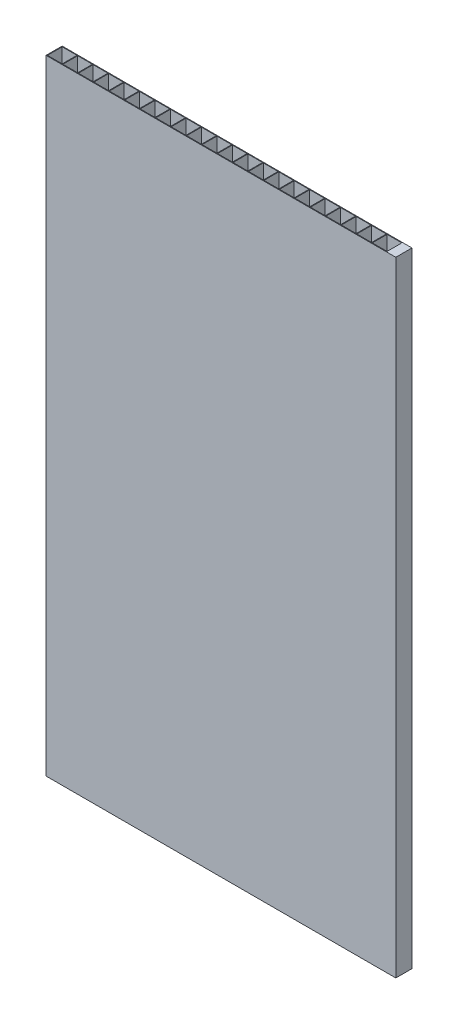
SolidWorks part; units mm, degrees
material "Perspex (TM) GS Acrylic Cast Sheet"
ref_plane "Front Plane" through (0, 0, 0) normal (0, 0, 1) x (1, 0, 0)
ref_plane "Top Plane" through (0, 0, 0) normal (0, 1, 0) x (1, 0, 0)
ref_plane "Right Plane" through (0, 0, 0) normal (1, 0, 0) x (0, 0, -1)
sketch "Sketch1" plane through (0, 0, 0) normal (0, 1, 0) x (1, 0, 0)
  line L0 (6, 5.75) -> (6, 0.25)
  line L1 (0, 0) -> (130, 0)
  line L2 (0, 0) -> (0, 6)
  line L3 (0, 6) -> (130, 6)
  line L4 (130, 0) -> (130, 6)
  line L5 (0.25, 5.75) -> (5.75, 5.75)
  line L6 (0.25, 5.75) -> (0.25, 0.25)
  line L7 (0.25, 0.25) -> (5.75, 0.25)
  line L8 (5.75, 5.75) -> (5.75, 0.25)
  line L9 (6, 5.75) -> (11.5, 5.75)
  line L10 (11.5, 5.75) -> (11.5, 0.25)
  line L11 (6, 0.25) -> (11.5, 0.25)
  line L12 (11.75, 5.75) -> (11.75, 0.25)
  line L13 (11.75, 5.75) -> (17.25, 5.75)
  line L14 (17.25, 5.75) -> (17.25, 0.25)
  line L15 (11.75, 0.25) -> (17.25, 0.25)
  line L16 (17.5, 5.75) -> (17.5, 0.25)
  line L17 (17.5, 5.75) -> (23, 5.75)
  line L18 (23, 5.75) -> (23, 0.25)
  line L19 (17.5, 0.25) -> (23, 0.25)
  line L20 (23.25, 5.75) -> (23.25, 0.25)
  line L21 (23.25, 5.75) -> (28.75, 5.75)
  line L22 (28.75, 5.75) -> (28.75, 0.25)
  line L23 (23.25, 0.25) -> (28.75, 0.25)
  line L24 (29, 5.75) -> (29, 0.25)
  line L25 (29, 5.75) -> (34.5, 5.75)
  line L26 (34.5, 5.75) -> (34.5, 0.25)
  line L27 (29, 0.25) -> (34.5, 0.25)
  line L28 (34.75, 5.75) -> (34.75, 0.25)
  line L29 (34.75, 5.75) -> (40.25, 5.75)
  line L30 (40.25, 5.75) -> (40.25, 0.25)
  line L31 (34.75, 0.25) -> (40.25, 0.25)
  line L32 (40.5, 5.75) -> (40.5, 0.25)
  line L33 (40.5, 5.75) -> (46, 5.75)
  line L34 (46, 5.75) -> (46, 0.25)
  line L35 (40.5, 0.25) -> (46, 0.25)
  line L36 (46.25, 5.75) -> (46.25, 0.25)
  line L37 (46.25, 5.75) -> (51.75, 5.75)
  line L38 (51.75, 5.75) -> (51.75, 0.25)
  line L39 (46.25, 0.25) -> (51.75, 0.25)
  line L40 (52, 5.75) -> (52, 0.25)
  line L41 (52, 5.75) -> (57.5, 5.75)
  line L42 (57.5, 5.75) -> (57.5, 0.25)
  line L43 (52, 0.25) -> (57.5, 0.25)
  line L44 (57.75, 5.75) -> (57.75, 0.25)
  line L45 (57.75, 5.75) -> (63.25, 5.75)
  line L46 (63.25, 5.75) -> (63.25, 0.25)
  line L47 (57.75, 0.25) -> (63.25, 0.25)
  line L48 (63.5, 5.75) -> (63.5, 0.25)
  line L49 (63.5, 5.75) -> (69, 5.75)
  line L50 (69, 5.75) -> (69, 0.25)
  line L51 (63.5, 0.25) -> (69, 0.25)
  line L52 (69.25, 5.75) -> (69.25, 0.25)
  line L53 (69.25, 5.75) -> (74.75, 5.75)
  line L54 (74.75, 5.75) -> (74.75, 0.25)
  line L55 (69.25, 0.25) -> (74.75, 0.25)
  line L56 (75, 5.75) -> (75, 0.25)
  line L57 (75, 5.75) -> (80.5, 5.75)
  line L58 (80.5, 5.75) -> (80.5, 0.25)
  line L59 (75, 0.25) -> (80.5, 0.25)
  line L60 (80.75, 5.75) -> (80.75, 0.25)
  line L61 (80.75, 5.75) -> (86.25, 5.75)
  line L62 (86.25, 5.75) -> (86.25, 0.25)
  line L63 (80.75, 0.25) -> (86.25, 0.25)
  line L64 (86.5, 5.75) -> (86.5, 0.25)
  line L65 (86.5, 5.75) -> (92, 5.75)
  line L66 (92, 5.75) -> (92, 0.25)
  line L67 (86.5, 0.25) -> (92, 0.25)
  line L68 (92.25, 5.75) -> (92.25, 0.25)
  line L69 (92.25, 5.75) -> (97.75, 5.75)
  line L70 (97.75, 5.75) -> (97.75, 0.25)
  line L71 (92.25, 0.25) -> (97.75, 0.25)
  line L72 (98, 5.75) -> (98, 0.25)
  line L73 (98, 5.75) -> (103.5, 5.75)
  line L74 (103.5, 5.75) -> (103.5, 0.25)
  line L75 (98, 0.25) -> (103.5, 0.25)
  line L76 (103.75, 5.75) -> (103.75, 0.25)
  line L77 (103.75, 5.75) -> (109.25, 5.75)
  line L78 (109.25, 5.75) -> (109.25, 0.25)
  line L79 (103.75, 0.25) -> (109.25, 0.25)
  line L80 (109.5, 5.75) -> (109.5, 0.25)
  line L81 (109.5, 5.75) -> (115, 5.75)
  line L82 (115, 5.75) -> (115, 0.25)
  line L83 (109.5, 0.25) -> (115, 0.25)
  line L84 (115.25, 5.75) -> (115.25, 0.25)
  line L85 (115.25, 5.75) -> (120.75, 5.75)
  line L86 (120.75, 5.75) -> (120.75, 0.25)
  line L87 (115.25, 0.25) -> (120.75, 0.25)
  line L88 (121, 5.75) -> (121, 0.25)
  line L89 (121, 5.75) -> (126.5, 5.75)
  line L90 (126.5, 5.75) -> (126.5, 0.25)
  line L91 (121, 0.25) -> (126.5, 0.25)
  line L160 (218.75, 5.75) -> (218.75, 0.25) [skipped]
  line L161 (218.75, 0.25) -> (224.25, 0.25) [skipped]
  line L162 (224.25, 5.75) -> (224.25, 0.25) [skipped]
  line L163 (218.75, 5.75) -> (224.25, 5.75) [skipped]
  line L164 (132.5, 5.75) -> (132.5, 0.25) [skipped]
  line L165 (132.5, 0.25) -> (138, 0.25) [skipped]
  line L166 (138, 5.75) -> (138, 0.25) [skipped]
  line L167 (132.5, 5.75) -> (138, 5.75) [skipped]
  line L168 (138.25, 5.75) -> (138.25, 0.25) [skipped]
  line L169 (138.25, 5.75) -> (143.75, 5.75) [skipped]
  line L170 (143.75, 5.75) -> (143.75, 0.25) [skipped]
  line L171 (138.25, 0.25) -> (143.75, 0.25) [skipped]
  line L172 (144, 5.75) -> (144, 0.25) [skipped]
  line L173 (144, 5.75) -> (149.5, 5.75) [skipped]
  line L174 (149.5, 5.75) -> (149.5, 0.25) [skipped]
  line L175 (144, 0.25) -> (149.5, 0.25) [skipped]
  line L176 (149.75, 5.75) -> (149.75, 0.25) [skipped]
  line L177 (149.75, 5.75) -> (155.25, 5.75) [skipped]
  line L178 (155.25, 5.75) -> (155.25, 0.25) [skipped]
  line L179 (149.75, 0.25) -> (155.25, 0.25) [skipped]
  line L180 (155.5, 5.75) -> (155.5, 0.25) [skipped]
  line L181 (155.5, 5.75) -> (161, 5.75) [skipped]
  line L182 (161, 5.75) -> (161, 0.25) [skipped]
  line L183 (155.5, 0.25) -> (161, 0.25) [skipped]
  line L184 (161.25, 5.75) -> (161.25, 0.25) [skipped]
  line L185 (161.25, 5.75) -> (166.75, 5.75) [skipped]
  line L186 (166.75, 5.75) -> (166.75, 0.25) [skipped]
  line L187 (161.25, 0.25) -> (166.75, 0.25) [skipped]
  line L188 (167, 5.75) -> (167, 0.25) [skipped]
  line L189 (167, 5.75) -> (172.5, 5.75) [skipped]
  line L190 (172.5, 5.75) -> (172.5, 0.25) [skipped]
  line L191 (167, 0.25) -> (172.5, 0.25) [skipped]
  line L192 (172.75, 5.75) -> (172.75, 0.25) [skipped]
  line L193 (172.75, 5.75) -> (178.25, 5.75) [skipped]
  line L194 (178.25, 5.75) -> (178.25, 0.25) [skipped]
  line L195 (172.75, 0.25) -> (178.25, 0.25) [skipped]
  line L196 (178.5, 5.75) -> (178.5, 0.25) [skipped]
  line L197 (178.5, 5.75) -> (184, 5.75) [skipped]
  line L198 (184, 5.75) -> (184, 0.25) [skipped]
  line L199 (178.5, 0.25) -> (184, 0.25) [skipped]
  line L200 (184.25, 5.75) -> (184.25, 0.25) [skipped]
  line L201 (184.25, 5.75) -> (189.75, 5.75) [skipped]
  line L202 (189.75, 5.75) -> (189.75, 0.25) [skipped]
  line L203 (184.25, 0.25) -> (189.75, 0.25) [skipped]
  line L204 (190, 5.75) -> (190, 0.25) [skipped]
  line L205 (190, 5.75) -> (195.5, 5.75) [skipped]
  line L206 (195.5, 5.75) -> (195.5, 0.25) [skipped]
  line L207 (190, 0.25) -> (195.5, 0.25) [skipped]
  line L208 (195.75, 5.75) -> (195.75, 0.25) [skipped]
  line L209 (195.75, 5.75) -> (201.25, 5.75) [skipped]
  line L210 (201.25, 5.75) -> (201.25, 0.25) [skipped]
  line L211 (195.75, 0.25) -> (201.25, 0.25) [skipped]
  line L212 (201.5, 5.75) -> (201.5, 0.25) [skipped]
  line L213 (201.5, 5.75) -> (207, 5.75) [skipped]
  line L214 (207, 5.75) -> (207, 0.25) [skipped]
  line L215 (201.5, 0.25) -> (207, 0.25) [skipped]
  line L216 (207.25, 5.75) -> (207.25, 0.25) [skipped]
  line L217 (207.25, 5.75) -> (212.75, 5.75) [skipped]
  line L218 (212.75, 5.75) -> (212.75, 0.25) [skipped]
  line L219 (207.25, 0.25) -> (212.75, 0.25) [skipped]
  line L220 (213, 5.75) -> (213, 0.25) [skipped]
  line L221 (213, 5.75) -> (218.5, 5.75) [skipped]
  line L222 (218.5, 5.75) -> (218.5, 0.25) [skipped]
  line L223 (213, 0.25) -> (218.5, 0.25) [skipped]
  line L224 (126.75, 5.75) -> (126.75, 0.25) [skipped]
  line L225 (126.75, 0.25) -> (132.25, 0.25) [skipped]
  line L226 (132.25, 5.75) -> (132.25, 0.25) [skipped]
  line L227 (126.75, 5.75) -> (132.25, 5.75) [skipped]
  point P9 (0.25, 3)
  point P10 (0, 3)
  dimension "D1" = 130
  dimension "D2" = 6
  dimension "D3" = 5.5
  dimension "D4" = 5.5
  dimension "D5" = 0.25
  dimension "D6" = 39
extrude "Boss-Extrude1" add sketch "Sketch1" along normal blind 232
